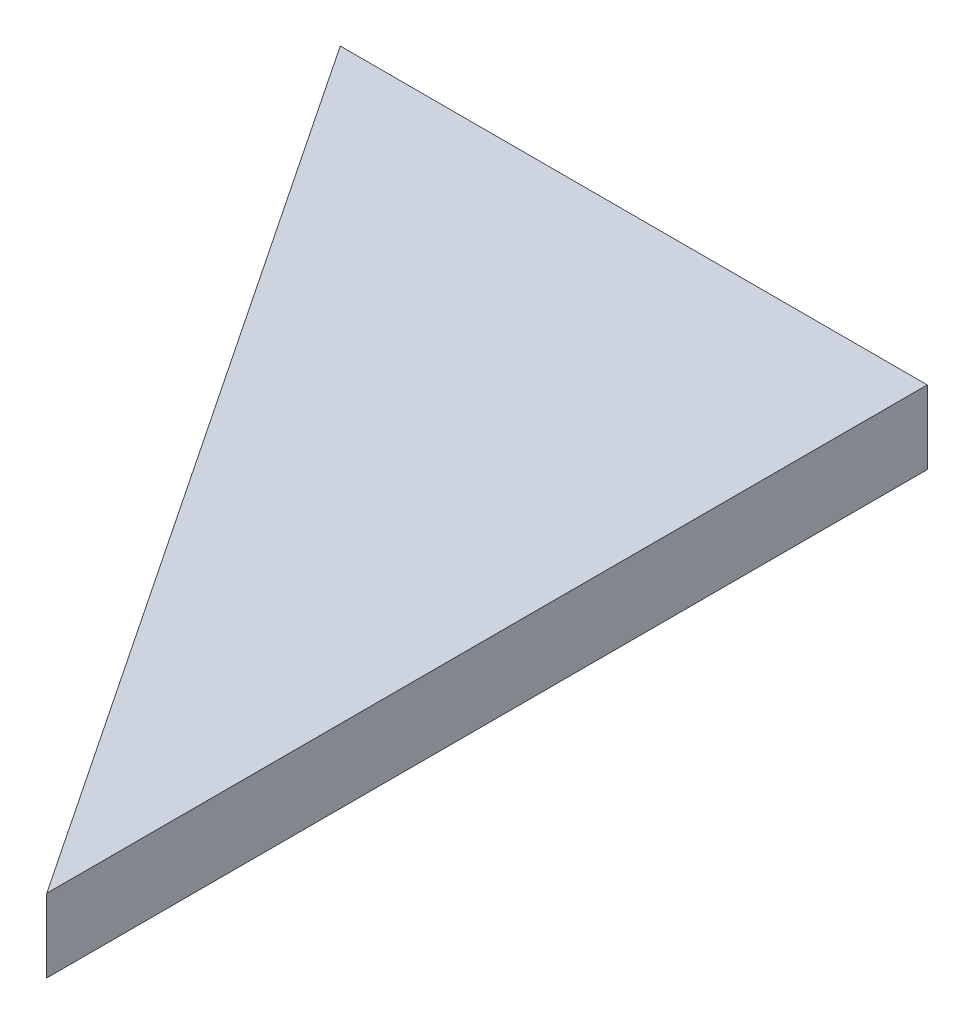
SolidWorks part; units mm, degrees
ref_plane "Front Plane" through (0, 0, 0) normal (0, 0, 1) x (1, 0, 0)
ref_plane "Top Plane" through (0, 0, 0) normal (0, 1, 0) x (1, 0, 0)
ref_plane "Right Plane" through (0, 0, 0) normal (1, 0, 0) x (0, 0, -1)
sketch "Sketch1" plane through (0, 0, 0) normal (0, 1, 0) x (1, 0, 0)
  line L0 (0, 0) -> (101.6, 0)
  line L1 (101.6, 0) -> (101.6, -152.4)
  line L2 (101.6, -152.4) -> (0, 0)
  dimension "D1" = 101.6
  dimension "D2" = 152.4
extrude "Boss-Extrude1" add sketch "Sketch1" along normal blind 12.7
